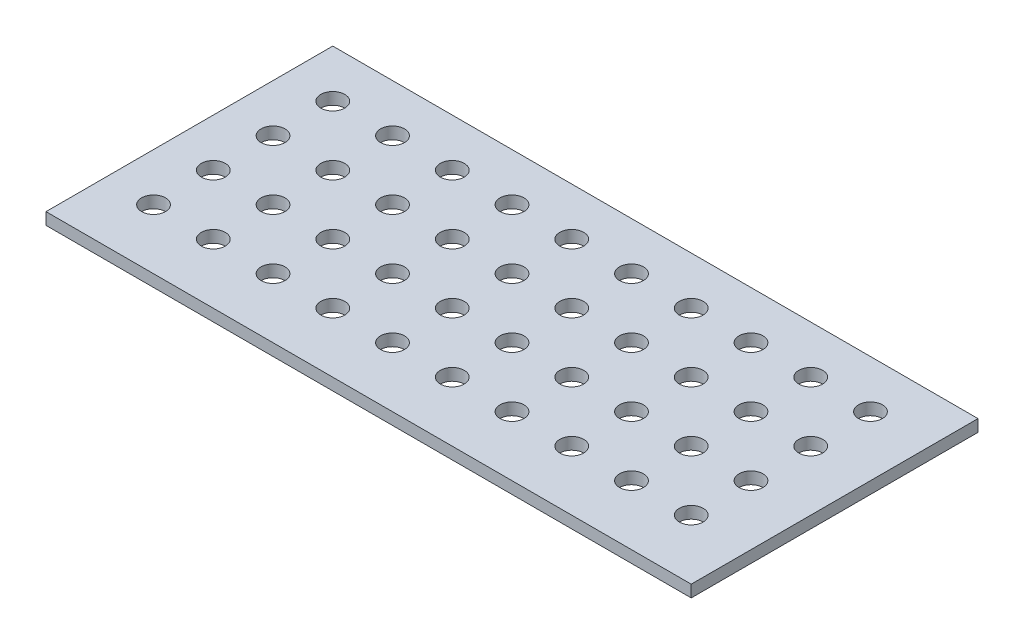
SolidWorks part; units mm, degrees
ref_plane "Front Plane" through (0, 0, 0) normal (0, 0, 1) x (1, 0, 0)
ref_plane "Top Plane" through (0, 0, 0) normal (0, 1, 0) x (1, 0, 0)
ref_plane "Right Plane" through (0, 0, 0) normal (1, 0, 0) x (0, 0, -1)
sketch "Sketch1" plane through (0, 0, 0) normal (0, 1, 0) x (1, 0, 0)
  line L0 (-342.9, 152.4) -> (-342.9, -152.4)
  line L1 (-381, 190.5) -> (381, 190.5)
  line L2 (-381, 190.5) -> (-381, -190.5)
  line L3 (-381, -190.5) -> (381, -190.5)
  line L4 (381, 190.5) -> (381, -190.5)
  line L5 (-381, 190.5) -> (381, -190.5) construction
  line L6 (-381, -190.5) -> (381, 190.5) construction
  line L7 (-342.9, -152.4) -> (342.9, -152.4)
  line L8 (342.9, 152.4) -> (342.9, -152.4)
  line L9 (-342.9, 152.4) -> (342.9, 152.4)
  point P0 (0, 0)
  dimension "D1" = 762
  dimension "D2" = 381
  dimension "D3" = 38.1
extrude "Boss-Extrude1" add sketch "Sketch1" along normal blind 12.7 contours L0 L7 L8 L9
sketch "Sketch2" plane through (0, 12.7, 0) normal (0, 1, 0) x (1, 0, 0)
  line L2 (0, 0) -> (138.4843, 0) construction
  circle A0 centre (-292.1, 101.6) radius 12.7
  circle A1 centre (-228.6, 101.6) radius 12.7
  circle A2 centre (-165.1, 101.6) radius 12.7
  circle A3 centre (-101.6, 101.6) radius 12.7
  circle A4 centre (-38.1, 101.6) radius 12.7
  circle A5 centre (25.4, 101.6) radius 12.7
  circle A6 centre (88.9, 101.6) radius 12.7
  circle A7 centre (152.4, 101.6) radius 12.7
  circle A8 centre (215.9, 101.6) radius 12.7
  circle A9 centre (279.4, 101.6) radius 12.7
  circle A10 centre (-228.6, 38.1) radius 12.7
  circle A11 centre (-165.1, 38.1) radius 12.7
  circle A12 centre (-101.6, 38.1) radius 12.7
  circle A13 centre (-38.1, 38.1) radius 12.7
  circle A14 centre (25.4, 38.1) radius 12.7
  circle A15 centre (88.9, 38.1) radius 12.7
  circle A16 centre (152.4, 38.1) radius 12.7
  circle A17 centre (215.9, 38.1) radius 12.7
  circle A18 centre (279.4, 38.1) radius 12.7
  circle A19 centre (-228.6, -25.4) radius 12.7
  circle A20 centre (-165.1, -25.4) radius 12.7
  circle A21 centre (-101.6, -25.4) radius 12.7
  circle A22 centre (-38.1, -25.4) radius 12.7
  circle A23 centre (25.4, -25.4) radius 12.7
  circle A24 centre (88.9, -25.4) radius 12.7
  circle A25 centre (152.4, -25.4) radius 12.7
  circle A26 centre (215.9, -25.4) radius 12.7
  circle A27 centre (279.4, -25.4) radius 12.7
  circle A28 centre (-228.6, -88.9) radius 12.7
  circle A29 centre (-165.1, -88.9) radius 12.7
  circle A30 centre (-101.6, -88.9) radius 12.7
  circle A31 centre (-38.1, -88.9) radius 12.7
  circle A32 centre (25.4, -88.9) radius 12.7
  circle A33 centre (88.9, -88.9) radius 12.7
  circle A34 centre (152.4, -88.9) radius 12.7
  circle A35 centre (215.9, -88.9) radius 12.7
  circle A36 centre (279.4, -88.9) radius 12.7
  circle A37 centre (-292.1, 38.1) radius 12.7
  circle A38 centre (-292.1, -25.4) radius 12.7
  circle A39 centre (-292.1, -88.9) radius 12.7
  dimension "D4" = 10
  dimension "D5" = 4
  dimension "D1" = 25.4
  dimension "D2" = 50.8
  dimension "D3" = 50.8
extrude "Cut-Extrude1" cut sketch "Sketch2" against normal through all
